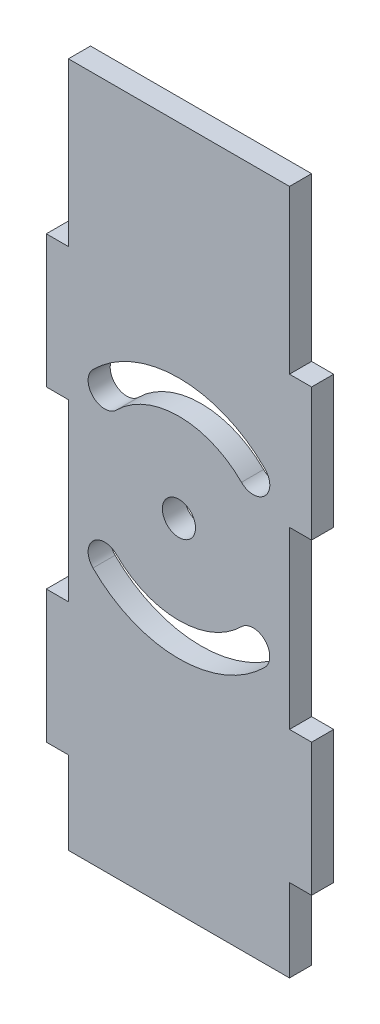
SolidWorks part; units mm, degrees
ref_plane "Front Plane" through (0, 0, 0) normal (0, 0, 1) x (1, 0, 0)
ref_plane "Top Plane" through (0, 0, 0) normal (0, 1, 0) x (1, 0, 0)
ref_plane "Right Plane" through (0, 0, 0) normal (1, 0, 0) x (0, 0, -1)
sketch "Sketch1" plane through (0, 0, 0) normal (0, 0, 1) x (1, 0, 0)
  line L0 (-38.1, 279.1906) -> (-38.1, 298.2406) construction
  line L1 (-3.175, 365.7785) -> (-34.925, 365.7785)
  line L2 (0, 342.4214) -> (0, 323.3714)
  line L3 (-3.175, 267.3188) -> (-34.925, 267.3188)
  line L4 (-38.1, 342.4214) -> (-38.1, 323.3714)
  line L5 (-38.1, 267.3188) -> (-34.925, 267.3188) construction
  line L6 (0, 279.1906) -> (0, 298.2406) construction
  line L7 (-3.175, 365.7785) -> (0, 365.7785) construction
  line L8 (-34.925, 267.3188) -> (-34.925, 279.1906) construction
  line L11 (0, 342.4214) -> (-3.175, 342.4214)
  line L12 (-3.175, 365.7785) -> (-3.175, 342.4214)
  line L13 (0, 323.3714) -> (-3.175, 323.3714)
  line L14 (-38.1, 298.2406) -> (-38.1, 279.1906)
  line L15 (0, 298.2406) -> (-3.175, 298.2406)
  line L16 (-3.175, 323.3714) -> (-3.175, 298.2406)
  line L17 (0, 279.1906) -> (-3.175, 279.1906)
  line L18 (0, 298.2406) -> (0, 279.1906)
  line L20 (-3.175, 279.1906) -> (-3.175, 267.3188)
  line L21 (-38.1, 279.1906) -> (-34.925, 279.1906)
  line L24 (-34.925, 279.1906) -> (-34.925, 267.3188)
  line L25 (-38.1, 323.3714) -> (-34.925, 323.3714)
  line L27 (-38.1, 298.2406) -> (-34.925, 298.2406)
  line L28 (-34.925, 323.3714) -> (-34.925, 298.2406)
  line L31 (-38.1, 342.4214) -> (-34.925, 342.4214)
  line L32 (-34.925, 365.7785) -> (-34.925, 342.4214)
  line L34 (-3.175, 267.3188) -> (-3.175, 279.1906) construction
  dimension "D1" = 0
  dimension "D2" = 0
extrude "Boss-Extrude1" add sketch "Sketch1" along normal blind 3.175 contours L1 L32 L31 L4 L25 L28 L27 L14 L21 L24 L3 L20 L17 L18 L15 L16 L13 L2 L11 L12
sketch "Sketch3" plane through (0, 0, 3.175) normal (0, 0, 1) x (1, 0, 0)
  line L0 (-19.05, 365.7785) -> (-19.05, 267.3188)
  line L1 (-3.175, 365.7785) -> (-34.925, 365.7785) construction
  line L2 (-3.175, 267.3188) -> (-34.925, 267.3188) construction
  line L3 (-19.05, 316.5487) -> (-3.175, 316.5487)
  line L4 (-3.175, 323.3714) -> (-3.175, 298.2406) construction
  line L5 (-29.7158, 327.2144) -> (-8.3859, 305.8846)
  line L6 (-8.3842, 327.2144) -> (-29.7141, 305.8846)
  circle A0 centre (-19.05, 316.5487) radius 2.3813
  arc A1 (-29.7158, 327.2144) -> (-8.3842, 327.2144) centre (-19.05, 316.5487) cw construction
  arc A2 (-6.7004, 328.8982) -> (-31.3996, 328.8982) centre (-19.05, 316.5487) ccw
  arc A3 (-10.068, 325.5306) -> (-28.032, 325.5306) centre (-19.05, 316.5487) ccw
  arc A4 (-10.068, 325.5306) -> (-6.7004, 328.8982) centre (-8.3842, 327.2144) ccw
  arc A5 (-31.3996, 328.8982) -> (-28.032, 325.5306) centre (-29.7158, 327.2144) ccw
  arc A6 (-29.7141, 305.8846) -> (-8.3859, 305.8846) centre (-19.05, 316.5487) ccw construction
  arc A7 (-31.3979, 304.2008) -> (-6.7021, 304.2008) centre (-19.05, 316.5487) ccw
  arc A8 (-28.0303, 307.5684) -> (-10.0697, 307.5684) centre (-19.05, 316.5487) ccw
  arc A9 (-28.0303, 307.5684) -> (-31.3979, 304.2008) centre (-29.7141, 305.8846) ccw
  arc A10 (-6.7021, 304.2008) -> (-10.0697, 307.5684) centre (-8.3859, 305.8846) ccw
  point P13 (-19.05, 331.6323)
  point P18 (-19.05, 301.4674)
  dimension "D1" = 4.7625
  dimension "D2" = 2.3813
  dimension "D3" = 2.3813
  dimension "D4" = 45
  dimension "D5" = 12.7024
  dimension "D6" = 12.7
extrude "Cut-Extrude2" cut sketch "Sketch3" against normal blind 3.175
